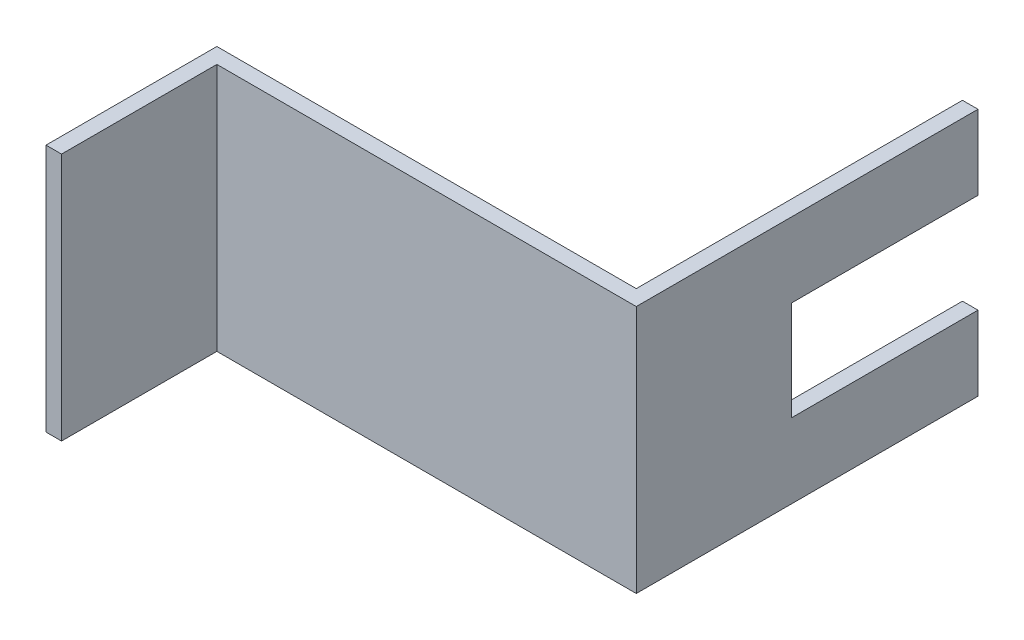
SolidWorks part; units mm, degrees
ref_plane "Front Plane" through (0, 0, 0) normal (0, 0, 1) x (1, 0, 0)
ref_plane "Top Plane" through (0, 0, 0) normal (0, 1, 0) x (1, 0, 0)
ref_plane "Right Plane" through (0, 0, 0) normal (1, 0, 0) x (0, 0, -1)
sketch "Sketch1" plane through (0, 0, 0) normal (0, 1, 0) x (1, 0, 0)
  line L0 (28.0639, 26.8591) -> (28.0639, -6.4784)
  line L1 (28.0639, -6.4784) -> (-14.7986, -6.4784)
  line L2 (-14.7986, -6.4784) -> (-14.7986, -23.9409)
  line L3 (-14.7986, -23.9409) -> (-13.2111, -23.9409)
  line L4 (-13.2111, -23.9409) -> (-13.2111, -8.0659)
  line L5 (-13.2111, -8.0659) -> (29.6514, -8.0659)
  line L6 (29.6514, -8.0659) -> (29.6514, 26.8591)
  line L7 (29.6514, 26.8591) -> (27.6947, 26.8591)
  line L8 (-14.7986, -23.9409) -> (-14.7986, -6.4784)
  line L10 (-14.7986, -23.9409) -> (-13.2111, -23.9409)
  line L11 (-14.7986, -23.9409) -> (-14.7986, -6.4784)
  line L12 (-14.7986, -6.4784) -> (-13.2111, -6.4784)
  line L13 (-13.2111, -23.9409) -> (-13.2111, -6.4784)
  line L14 (29.6514, -8.0659) -> (28.0639, -8.0659)
  line L15 (29.6514, -8.0659) -> (29.6514, 26.8591)
  line L16 (29.6514, 26.8591) -> (28.0639, 26.8591)
  line L17 (28.0639, -8.0659) -> (28.0639, 26.8591)
  line L18 (28.0639, -6.4784) -> (-13.2111, -6.4784)
  line L19 (28.0639, -6.4784) -> (28.0639, -8.0659)
  line L20 (28.0639, -8.0659) -> (-13.2111, -8.0659)
  line L21 (-13.2111, -6.4784) -> (-13.2111, -8.0659)
  dimension "D1" = 1.5875
  dimension "D2" = 1.5875
  dimension "D3" = 1.5875
  dimension "D4" = 44.45
  dimension "D5" = 15.875
  dimension "D6" = 50.8
extrude "Boss-Extrude1" add sketch "Sketch1" along normal blind 25.4 contours L4 L13 L1 L2 L3 | L5 L17 L1 L13 | L17 L5 L6 L7 L16 L0
sketch "Sketch2" plane through (29.6514, 0, 0) normal (1, 0, 0) x (0, 0, -1)
  line L0 (26.8591, 25.4) -> (26.8591, 0) construction
  line L1 (26.8591, 17.78) -> (7.8091, 17.78)
  line L2 (26.8591, 17.78) -> (26.8591, 7.62)
  line L3 (26.8591, 7.62) -> (7.8091, 7.62)
  line L4 (7.8091, 17.78) -> (7.8091, 7.62)
  line L5 (-8.0659, 25.4) -> (26.8591, 25.4) construction
  dimension "D1" = 10.16
  dimension "D2" = 7.62
  dimension "D3" = 19.05
extrude "Cut-Extrude1" cut sketch "Sketch2" against normal blind 25.4
